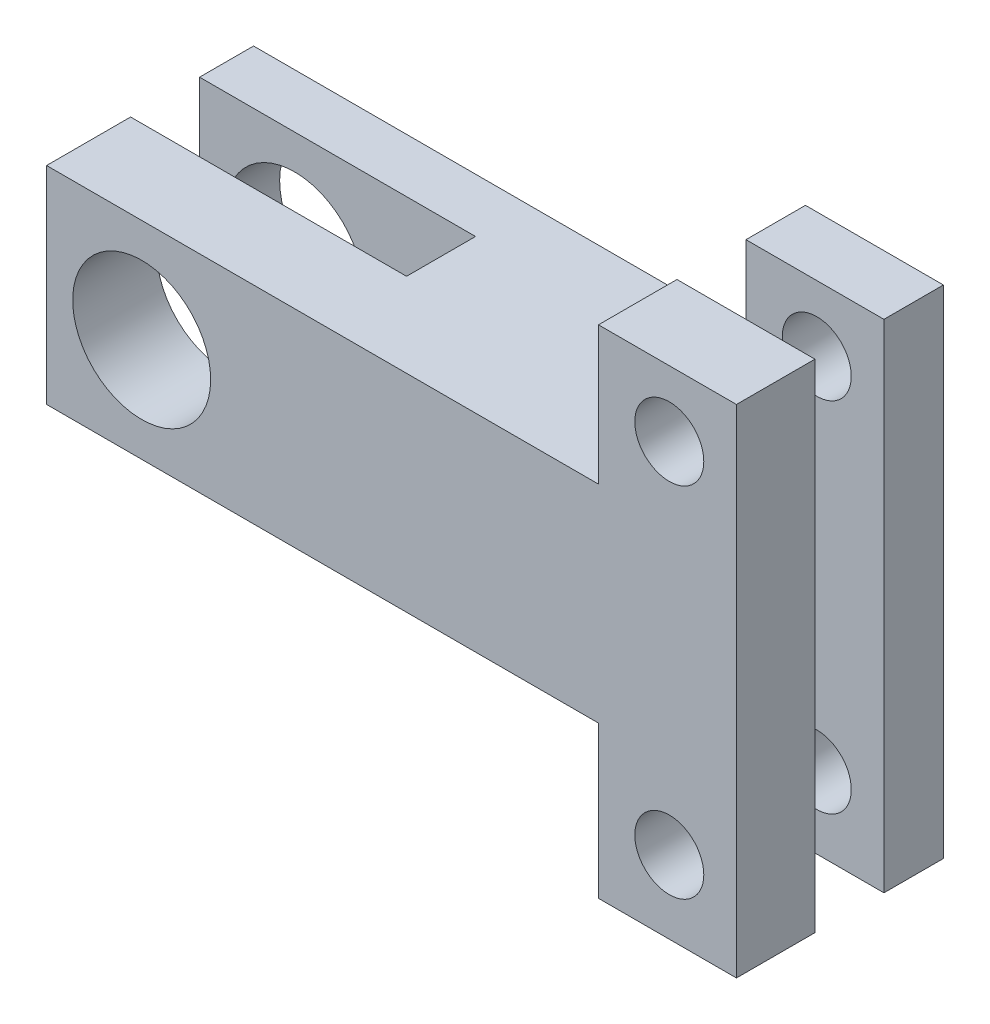
SolidWorks part; units mm, degrees
ref_plane "Front Plane" through (0, 0, 0) normal (0, 0, 1) x (1, 0, 0)
ref_plane "Top Plane" through (0, 0, 0) normal (0, 1, 0) x (1, 0, 0)
ref_plane "Right Plane" through (0, 0, 0) normal (1, 0, 0) x (0, 0, -1)
sketch "Sketch1" plane through (0, 0, 0) normal (0, 0, 1) x (1, 0, 0)
  line L1 (-25, -7.5) -> (25, -7.5)
  line L2 (-25, -7.5) -> (-25, 7.5)
  line L3 (-25, 7.5) -> (25, 7.5)
  line L4 (25, -7.5) -> (25, 7.5)
  line L5 (-25, -7.5) -> (25, 7.5) construction
  line L6 (-25, 7.5) -> (25, -7.5) construction
  point P0 (0, 0)
  dimension "D1" = 50
  dimension "D2" = 15
extrude "Boss-Extrude1" add sketch "Sketch1" along normal blind 15
sketch "Sketch3" plane through (0, 7.5, 0) normal (0, 1, 0) x (1, 0, 0)
  line L0 (-25, -3.9114) -> (-5, -3.9114)
  line L1 (-25, -15) -> (-25, 0) construction
  line L2 (-5, -3.9114) -> (-5, -8.9114)
  line L3 (-5, -8.9114) -> (-25, -8.9114)
  line L4 (-25, -8.9114) -> (-25, -3.9114)
  dimension "D1" = 5
  dimension "D2" = 20
extrude "Cut-Extrude1" cut sketch "Sketch3" against normal blind 30
sketch "Sketch5" plane through (0, 0, 15) normal (0, 0, 1) x (1, 0, 0)
  circle A0 centre (-18.1083, 0) radius 5
  dimension "D1" = 10
extrude "Cut-Extrude2" cut sketch "Sketch5" against normal blind 30
sketch "Sketch7" plane through (0, 7.5, 0) normal (0, 1, 0) x (1, 0, 0)
  line L0 (15, 0) -> (25, 0)
  line L1 (25, 0) -> (-25, 0) construction
  line L2 (25, 0) -> (25, -15)
  line L3 (25, -15) -> (25, 0) construction
  line L4 (25, -15) -> (15, -15)
  line L5 (25, -15) -> (-25, -15) construction
  line L6 (15, -15) -> (15, 0)
  dimension "D1" = 10
extrude "Boss-Extrude2" add sketch "Sketch7" along normal blind 10
sketch "Sketch11" plane through (0, -7.5, 0) normal (0, -1, 0) x (1, 0, 0)
  line L0 (15, 15) -> (25, 15)
  line L1 (-25, 15) -> (25, 15) construction
  line L2 (25, 15) -> (25, 0)
  line L3 (25, 0) -> (15, 0)
  line L4 (-25, 0) -> (25, 0) construction
  line L5 (15, 0) -> (15, 15)
  dimension "D1" = 10
extrude "Boss-Extrude5" add sketch "Sketch11" along normal blind 11
sketch "Sketch12" plane through (0, 0, 15) normal (0, 0, 1) x (1, 0, 0)
  circle A0 centre (20.1321, 12.735) radius 2.5
  circle A1 centre (20.1321, -13.2024) radius 2.5
  dimension "D1" = 5
  dimension "D2" = 5
extrude "Cut-Extrude3" cut sketch "Sketch12" against normal blind 25
sketch "Sketch13" plane through (25, 0, 0) normal (1, 0, 0) x (0, 0, -1)
  line L0 (-9.3108, 17.5) -> (-9.3108, -18.5)
  line L1 (-15, 17.5) -> (0, 17.5) construction
  line L2 (0, -18.5) -> (-15, -18.5) construction
  line L3 (-9.3108, -18.5) -> (-4.3108, -18.5)
  line L4 (-4.3108, -18.5) -> (-4.3108, 17.5)
  line L5 (-4.3108, 17.5) -> (-9.3108, 17.5)
  dimension "D1" = 5
extrude "Cut-Extrude4" cut sketch "Sketch13" against normal blind 10
